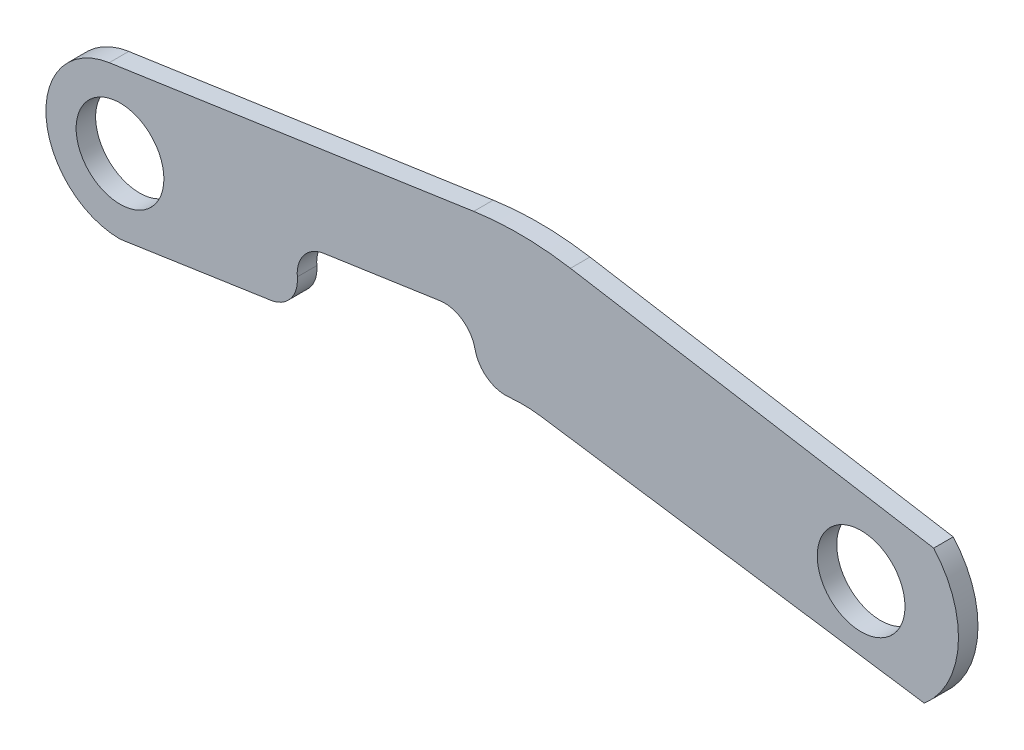
SolidWorks part; units mm, degrees
ref_plane "Front Plane" through (0, 0, 0) normal (0, 0, 1) x (1, 0, 0)
ref_plane "Top Plane" through (0, 0, 0) normal (0, 1, 0) x (1, 0, 0)
ref_plane "Right Plane" through (0, 0, 0) normal (1, 0, 0) x (0, 0, -1)
sketch "Sketch1" plane through (0, 0, 0) normal (0, 0, 1) x (1, 0, 0)
  line L7 (-244.8034, 23.8009) -> (-110.363, 43.5291)
  line L8 (-110.363, 43.5291) -> (23.636, 21.1397)
  line L10 (-110.363, -4.7309) -> (20.574, -24.13)
  line L11 (-124.3095, -6.8049) -> (-127.0669, 11.9858)
  line L12 (-127.0669, 11.9858) -> (-184.9965, 3.485)
  line L13 (-184.9965, 3.485) -> (-182.1862, -15.4122)
  line L14 (-110.363, -4.7309) -> (-124.3095, -6.8049)
  line L15 (-182.1862, -15.4122) -> (-241.3, -24.2034)
  line L16 (-241.3, -0.0734) -> (0, 0) construction
  circle A2 centre (-241.3, -0.0734) radius 14.2875
  circle A3 centre (0, 0) radius 14.2875
  arc A6 (-244.8034, 23.8009) -> (-241.3, -24.2034) centre (-241.3, -0.0734) ccw
  arc A7 (23.636, 21.1397) -> (20.574, -24.13) centre (0, 0) cw
  dimension "D1" = 48.26
  dimension "D2" = 28.575
  dimension "D3" = 28.575
  dimension "D4" = 135.8566
  dimension "D5" = 241.3
extrude "Boss-Extrude1" add sketch "Sketch1" along normal blind 6.35
fillet "Fillet2" radius 101.6 1 edges at (-110.363, 43.5291, 3.175)
fillet "Fillet4" radius 10.16 1 edges at (-127.0669, 11.9858, 3.175)
fillet "Fillet5" radius 10.16 1 edges at (-184.9965, 3.485, 3.175)
fillet "Fillet6" radius 10.16 1 edges at (-182.1862, -15.4122, 3.175)
fillet "Fillet7" radius 43.18 1 edges at (-110.363, -4.7309, 3.175)
fillet "Fillet8" radius 10.16 1 edges at (-124.3095, -6.8049, 3.175)
